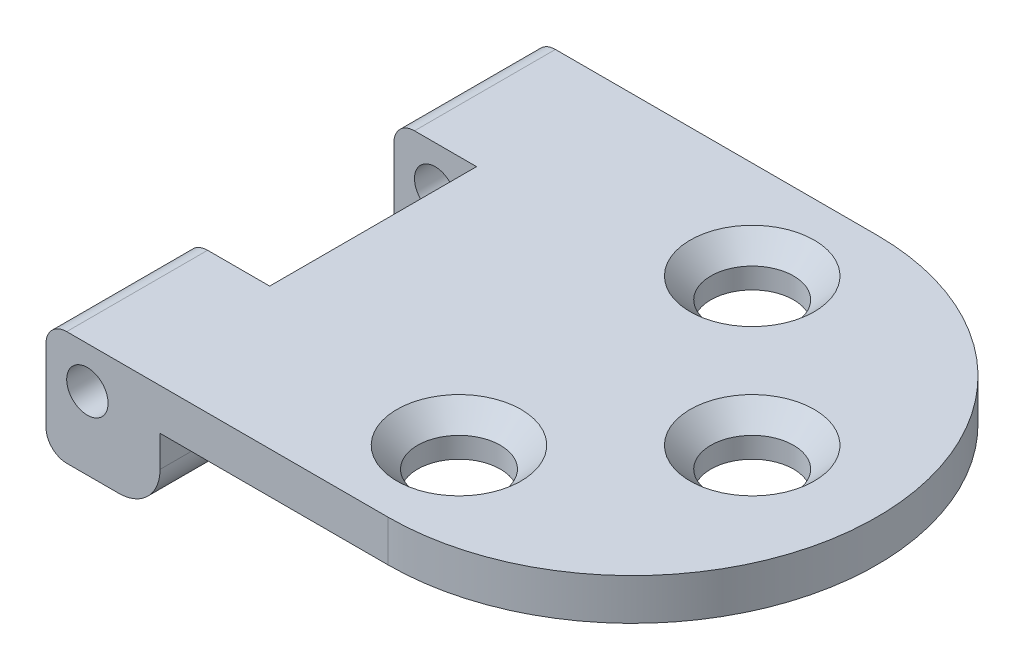
SolidWorks part; units mm, degrees
ref_plane "Front Plane" through (0, 0, 0) normal (0, 0, 1) x (1, 0, 0)
ref_plane "Top Plane" through (0, 0, 0) normal (0, 1, 0) x (1, 0, 0)
ref_plane "Right Plane" through (0, 0, 0) normal (1, 0, 0) x (0, 0, -1)
sketch "Sketch1" plane through (0, 0, 0) normal (0, 1, 0) x (1, 0, 0)
  line L1 (0, 0) -> (21, 0)
  line L2 (0, 0) -> (0, 30)
  line L3 (0, 30) -> (21, 30)
  arc A0 (21, 30) -> (21, 0) centre (21, 15) cw
  dimension "D1" = 21
  dimension "D2" = 30
extrude "Boss-Extrude1" add sketch "Sketch1" along normal blind 7
sketch "Sketch2" plane through (0, 0, 0) normal (0, -1, 0) x (1, 0, 0)
  line L0 (0, 0) -> (21, 0) construction
  line L1 (7, 0) -> (36.2161, 0)
  line L2 (7, 0) -> (7, -30)
  line L3 (7, -30) -> (36.2161, -30)
  line L4 (36.2161, 0) -> (36.2161, -30)
  line L6 (21, -30) -> (0, -30) construction
  line L7 (0, -30) -> (0, 0) construction
  dimension "D1" = 7
extrude "Cut-Extrude1" cut sketch "Sketch2" against normal offset from surface (4.46 mm away) 2.54 contours L1 L4 L3 L2 up to face at (14.25, 7, -15)
fillet "Fillet1" radius 2.54 1 edges at (7, 0, -15)
fillet "Fillet2" radius 1.27 2 edges at (0, 0, -15) (0, 7, -15)
sketch "Sketch3" plane through (0, 7, 0) normal (0, 1, 0) x (1, 0, 0)
  line L0 (0, 0) -> (0, 30) construction
  line L1 (0, 21.35) -> (5.08, 21.35)
  line L2 (0, 21.35) -> (0, 8.65)
  line L3 (0, 8.65) -> (5.08, 8.65)
  line L4 (5.08, 21.35) -> (5.08, 8.65)
  line L5 (5.08, 15) -> (-1.9964, 15) construction
  line L6 (0, 15) -> (-2.9477, 15) construction
  line L11 (63.4007, 15) -> (-6.7007, 15) construction
  circle A0 centre (28.35, 15) radius 2.54
  circle A1 centre (19.35, 24) radius 2.54
  circle A2 centre (19.35, 6) radius 2.54
  dimension "D3" = 28.35
  dimension "D4" = 19.35
  dimension "D5" = 9
  dimension "D7" = 5.08
  dimension "D1" = 5.08
  dimension "D2" = 12.7
  dimension "D6" = 9
extrude "Cut-Extrude2" cut sketch "Sketch3" against normal up to next
chamfer "Chamfer1" distance 1.27 angle 45 3 edges at (19.35, 7, -8.54) (28.35, 7, -12.46) (19.35, 7, -21.46)
sketch "Sketch4" plane through (0, 0, 0) normal (0, 0, 1) x (1, 0, 0)
  line L0 (0, 5.73) -> (0, 1.27) construction
  line L1 (1.27, 7) -> (21, 7) construction
  circle A0 centre (2.54, 4.46) radius 1.27
  dimension "D1" = 2.54
  dimension "D2" = 2.54
  dimension "D3" = 2.54
extrude "Cut-Extrude3" cut sketch "Sketch4" against normal through all
